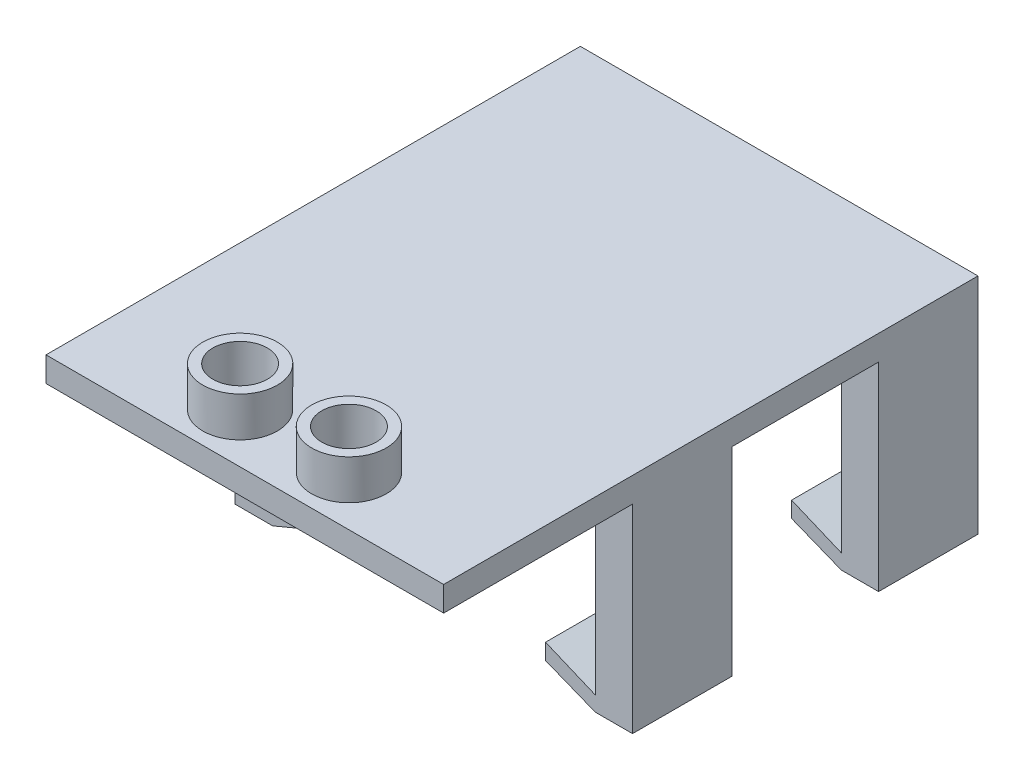
SolidWorks part; units mm, degrees
material "Custom Plastic"
ref_plane "Front Plane" through (0, 0, 0) normal (0, 0, 1) x (1, 0, 0)
ref_plane "Top Plane" through (0, 0, 0) normal (0, 1, 0) x (1, 0, 0)
ref_plane "Right Plane" through (0, 0, 0) normal (1, 0, 0) x (0, 0, -1)
sketch "Sketch3" plane through (0, 0, 0) normal (0, 1, 0) x (1, 0, 0)
  line L0 (29.1227, -39.629) -> (18.8853, -29.3915) construction
  line L1 (-11.5173, 12.441) -> (29.1227, 12.441)
  line L2 (-11.5173, 12.441) -> (-11.5173, -42.169)
  line L3 (-11.5173, -42.169) -> (18.8853, -42.169)
  line L4 (29.1227, 12.441) -> (29.1227, -34.5642)
  line L6 (21.4177, -26.8591) -> (29.1227, -34.5642) construction
  line L12 (18.8853, -42.169) -> (29.1227, -42.169)
  line L13 (29.1227, -42.169) -> (29.1227, -34.5642)
  circle A0 centre (3.2401, -37.089) radius 2.7813
  circle A2 centre (14.3653, -37.089) radius 2.7813
  dimension "D2" = 5.5626
  dimension "D3" = 5.5626
  dimension "D1" = 5.08
  dimension "1" = 40.64
  dimension "D4" = 11.1252
  dimension "D7" = 5.08
  dimension "D9" = 135
  dimension "D10" = 14.478
  dimension "D11" = 3.5814
extrude "Boss-Extrude3" add sketch "Sketch3" along normal blind 2.54
sketch "Sketch4" plane through (0, 0, 0) normal (0, -1, 0) x (1, 0, 0)
  line L0 (-11.5173, -12.441) -> (-11.5173, 42.169) construction
  line L1 (-11.5173, 27.945) -> (-7.7073, 27.945)
  line L2 (-11.5173, 27.945) -> (-11.5173, -12.441)
  line L3 (-11.5173, -12.441) -> (-7.7073, -12.441)
  line L4 (-7.7073, 27.945) -> (-7.7073, -12.441)
  line L5 (29.1227, -12.441) -> (-11.5173, -12.441) construction
  line L6 (-11.5173, 42.169) -> (29.1227, 42.169) construction
  line L7 (29.1227, 42.169) -> (29.1227, -12.441) construction
  line L8 (29.1227, 27.945) -> (25.3127, 27.945)
  line L9 (29.1227, 27.945) -> (29.1227, -12.441)
  line L10 (29.1227, -12.441) -> (25.3127, -12.441)
  line L11 (25.3127, 27.945) -> (25.3127, -12.441)
  dimension "D1" = 14.224
  dimension "D2" = 3.81
  dimension "D3" = 14.224
  dimension "D4" = 3.81
extrude "Boss-Extrude4" add sketch "Sketch4" along normal blind 20.32
sketch "Sketch5" plane through (-7.7073, 0, 0) normal (1, 0, 0) x (0, 0, -1)
  line L0 (-27.945, -20.32) -> (-27.945, 0) construction
  line L1 (-27.945, -18.796) -> (12.441, -18.796)
  line L2 (-27.945, -18.796) -> (-27.945, -20.32)
  line L3 (-27.945, -20.32) -> (12.441, -20.32)
  line L4 (12.441, -18.796) -> (12.441, -20.32)
  dimension "D1" = 1.524
extrude "Boss-Extrude5" add sketch "Sketch5" along normal blind 5.08
sketch "Sketch6" plane through (25.3127, 0, 0) normal (-1, 0, 0) x (0, 0, 1)
  line L0 (-12.441, 2.54) -> (-12.441, -20.32) construction
  line L1 (-12.441, -18.796) -> (27.945, -18.796)
  line L2 (-12.441, -18.796) -> (-12.441, -20.32)
  line L3 (-12.441, -20.32) -> (27.945, -20.32)
  line L4 (27.945, -18.796) -> (27.945, -20.32)
  dimension "D1" = 1.524
extrude "Boss-Extrude6" add sketch "Sketch6" along normal blind 5.08
sketch "Sketch7" plane through (0, 0, 27.945) normal (0, 0, 1) x (1, 0, 0)
  line L1 (-11.5173, 0) -> (29.1227, 0)
  line L2 (-11.5173, 0) -> (-11.5173, -20.32)
  line L3 (-11.5173, -20.32) -> (29.1227, -20.32)
  line L4 (29.1227, 0) -> (29.1227, -20.32)
extrude "Cut-Extrude1" cut sketch "Sketch7" against normal blind 5.08
sketch "Sketch11" plane through (0, 0, 0) normal (0, -1, 0) x (1, 0, 0)
  line L1 (-11.5173, 22.865) -> (29.1227, 22.865)
  line L2 (-11.5173, 22.865) -> (-11.5173, -12.441)
  line L3 (-11.5173, -12.441) -> (29.1227, -12.441)
  line L4 (29.1227, 22.865) -> (29.1227, -12.441)
extrude "Boss-Extrude7" add sketch "Sketch11" along normal blind 2.9718
sketch "Sketch12" plane through (0, 0, 22.865) normal (0, 0, 1) x (1, 0, 0)
  line L0 (-7.7073, -18.796) -> (-2.5934, -16.6688)
  line L1 (-2.5934, -16.6688) -> (-2.6273, -18.796)
  line L2 (-2.6273, -18.796) -> (-7.7073, -18.796)
  line L3 (20.2327, -18.796) -> (20.2327, -16.6688)
  line L4 (20.2327, -16.6688) -> (25.3127, -18.796)
  line L5 (25.3127, -18.796) -> (20.2327, -18.796)
  dimension "D1" = 2.1272
  dimension "D2" = 2.1272
extrude "Boss-Extrude8" add sketch "Sketch12" against normal up to surface (35.306 mm away) up to face at (8.8027, -13.1106, -12.441)
sketch "Sketch8" plane through (29.1227, 0, 0) normal (1, 0, 0) x (0, 0, -1)
  line L0 (12.441, -20.32) -> (-22.865, -20.32) construction
  line L1 (2.281, -20.32) -> (-12.705, -20.32)
  line L2 (2.281, -20.32) -> (2.281, 0)
  line L3 (2.281, 0) -> (-12.705, 0)
  line L4 (-12.705, -20.32) -> (-12.705, 0)
  line L5 (-42.169, 0) -> (-22.865, 0) construction
  line L6 (-22.865, -20.32) -> (-22.865, 0) construction
  line L7 (12.441, 2.54) -> (12.441, -20.32) construction
  dimension "D1" = 0
  dimension "D2" = 10.16
  dimension "D3" = 10.16
extrude "Cut-Extrude2" cut sketch "Sketch8" against normal through all
sketch "Sketch13" plane through (0, 0, 22.865) normal (0, 0, 1) x (1, 0, 0)
  line L0 (-7.6607, -20.32) -> (-2.618, -18.2165)
  line L1 (-11.5173, -20.32) -> (-2.6273, -20.32) construction
  line L2 (-2.6273, -18.796) -> (-2.5934, -16.6688) construction
  line L3 (-2.618, -18.2165) -> (-2.6273, -20.32)
  line L4 (-2.6273, -20.32) -> (-7.6607, -20.32)
  line L5 (20.2327, -20.32) -> (20.2048, -20.32)
  line L6 (20.2327, -20.32) -> (29.1227, -20.32) construction
  line L7 (20.2048, -20.32) -> (20.2327, -18.2946)
  line L8 (20.2327, -20.32) -> (20.2327, -16.6688) construction
  line L9 (20.2327, -18.2946) -> (20.2327, -20.32)
  line L10 (20.2327, -18.2946) -> (25.3127, -20.32)
  line L11 (25.3127, -20.32) -> (20.2327, -20.32)
  point P13 (0, 0)
  line M5 (20.2327, -16.6688) -> (20.2327, -20.32)
  line M6 (20.2327, -20.32) -> (29.1227, -20.32)
  line M10 (-11.5173, -20.32) -> (-2.6273, -20.32)
  line M11 (-2.6273, -20.32) -> (-2.6273, -18.796)
  line M12 (-2.6273, -18.796) -> (-2.5934, -16.6688)
  dimension "D1" = 2.1035
  dimension "D2" = 2.0254
extrude "Cut-Extrude3" cut sketch "Sketch13" against normal through all contours L0 M10 M11 M12 | L10 M5 M6
sketch "Sketch14" plane through (0, 0, 0) normal (0, -1, 0) x (1, 0, 0)
  circle A0 centre (3.2401, 37.089) radius 2.7813
  circle A1 centre (14.3653, 37.089) radius 2.7813
  circle A2 centre (3.2401, 37.089) radius 3.81
  circle A3 centre (14.3653, 37.089) radius 3.81
  dimension "D1" = 5.5626
  dimension "D2" = 5.5626
  dimension "D3" = 7.62
  dimension "D4" = 7.62
extrude "Boss-Extrude9" add sketch "Sketch14" against normal blind 6.604
sketch "Sketch15" plane through (0, 2.54, 0) normal (0, 1, 0) x (1, 0, 0)
  line L0 (18.8853, -42.169) -> (13.6783, -42.169) construction
  line L1 (-11.5173, -42.169) -> (29.1227, -42.169) construction
  line L2 (13.6783, -42.169) -> (29.1227, -42.169)
  line L4 (13.6783, -42.169) -> (18.8853, -39.4766)
  line L7 (13.6783, -42.169) -> (29.1227, -34.1831)
  line L8 (29.1227, -42.169) -> (29.1227, 12.441) construction
  line L9 (29.1227, -42.169) -> (29.1227, -34.1831)
  line L10 (8.8027, 12.441) -> (8.8027, -50.2652) construction
  line L11 (29.1227, 12.441) -> (-11.5173, 12.441) construction
  line L12 (3.9272, -42.169) -> (-11.5173, -34.1831)
  line L13 (-11.5173, -42.169) -> (-11.5173, -34.1831)
  line L14 (3.9272, -42.169) -> (-11.5173, -42.169)
  line M6 (-11.5173, -42.169) -> (29.1227, -42.169)
  line M10 (29.1227, -42.169) -> (29.1227, 12.441)
extrude "Cut-Extrude4" [suppressed] cut sketch "Sketch15" against normal through all contours L7 L4 M6 M10
equation "\"D3@Sketch8\"=\"D2@Sketch8\""
